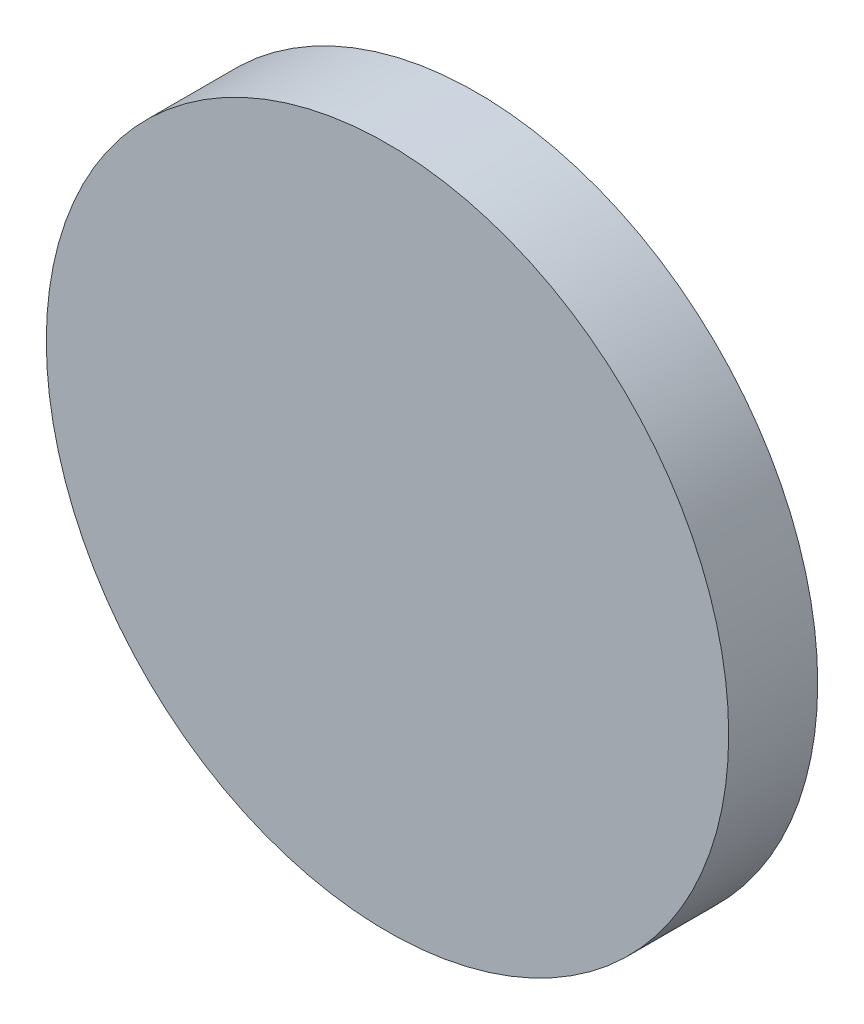
SolidWorks part; units mm, degrees
ref_plane "Front Plane" through (0, 0, 0) normal (0, 0, 1) x (1, 0, 0)
ref_plane "Top Plane" through (0, 0, 0) normal (0, 1, 0) x (1, 0, 0)
ref_plane "Right Plane" through (0, 0, 0) normal (1, 0, 0) x (0, 0, -1)
sketch "Sketch1" plane through (0, 0, 0) normal (0, 0, 1) x (1, 0, 0)
  circle A0 centre (0, 0) radius 11.5
  dimension "D1" = 23
extrude "Boss-Extrude1" add sketch "Sketch1" along normal blind 3
